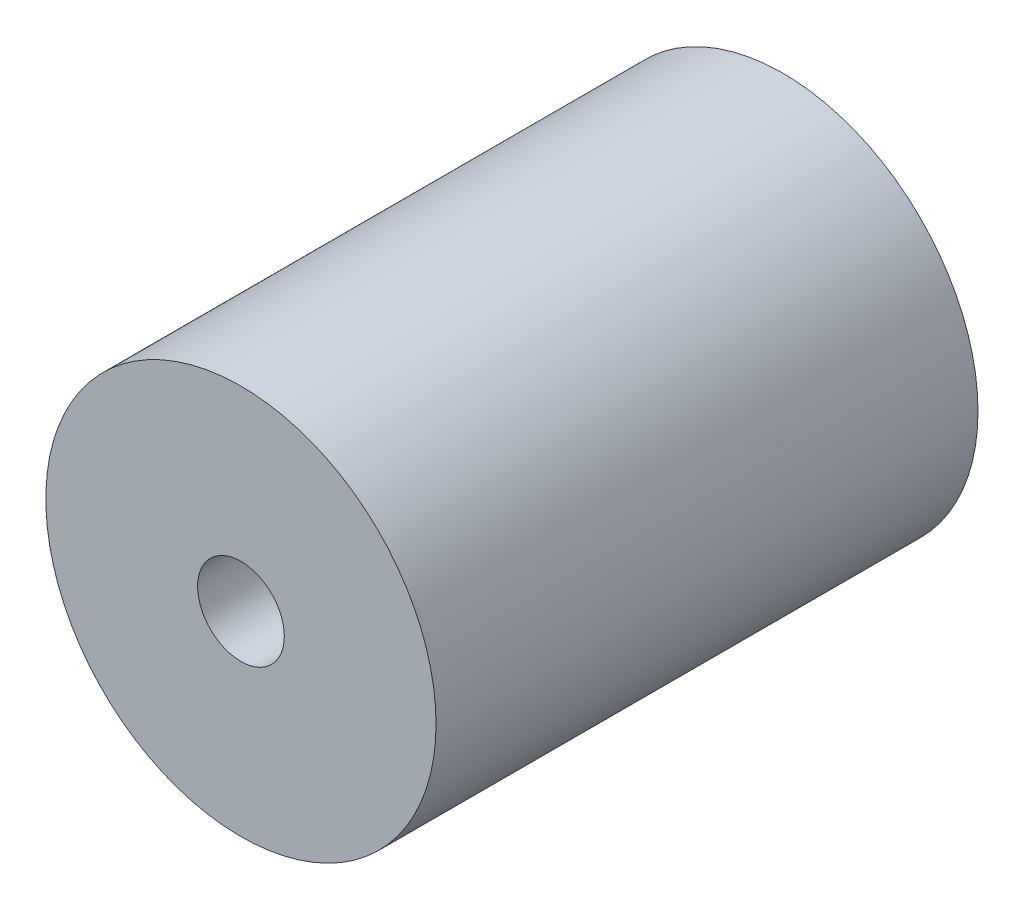
SolidWorks part; units mm, degrees
ref_plane "Front Plane" through (0, 0, 0) normal (0, 0, 1) x (1, 0, 0)
ref_plane "Top Plane" through (0, 0, 0) normal (0, 1, 0) x (1, 0, 0)
ref_plane "Right Plane" through (0, 0, 0) normal (1, 0, 0) x (0, 0, -1)
sketch "Sketch1" plane through (0, 0, 0) normal (0, 0, 1) x (1, 0, 0)
  circle A0 centre (0, 0) radius 9
  dimension "D1" = 18
extrude "Boss-Extrude1" add sketch "Sketch1" along normal mid plane 25 contours A0
sketch "Sketch2" plane through (0, 0, 12.5) normal (0, 0, 1) x (1, 0, 0)
  circle A0 centre (0, 0) radius 2
  dimension "D1" = 4
extrude "Cut-Extrude1" cut sketch "Sketch2" against normal up to surface (12.5 mm away)
sketch "Sketch3" plane through (0, 0, -12.5) normal (0, 0, -1) x (-1, 0, 0)
  circle A0 centre (0, 0) radius 4
  dimension "D1" = 8
extrude "Cut-Extrude2" cut sketch "Sketch3" against normal up to surface (12.5 mm away)
